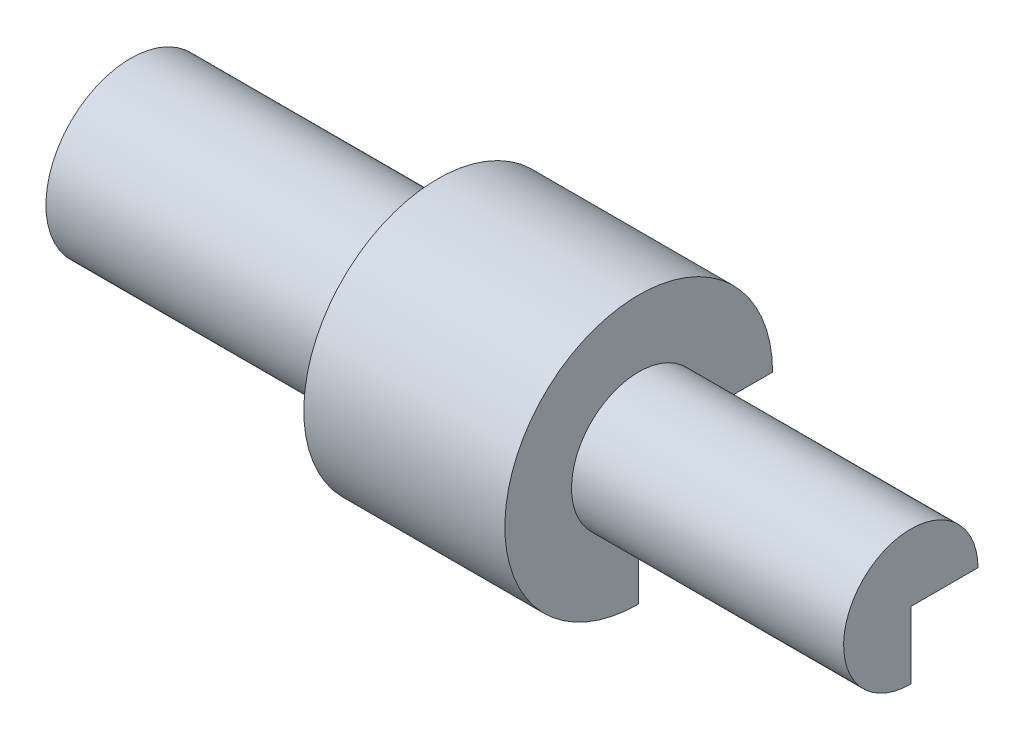
SolidWorks part; units mm, degrees
ref_plane "Front Plane" through (0, 0, 0) normal (0, 0, 1) x (1, 0, 0)
ref_plane "Top Plane" through (0, 0, 0) normal (0, 1, 0) x (1, 0, 0)
ref_plane "Right Plane" through (0, 0, 0) normal (1, 0, 0) x (0, 0, -1)
sketch "Sketch1" plane through (0, 0, 0) normal (0, 1, 0) x (1, 0, 0)
  line L0 (0, 0) -> (0, 32.5503)
  line L1 (0, 32.5503) -> (118.0212, 32.5503)
  line L2 (118.0212, 51.4505) -> (195.3021, 51.4505)
  line L3 (195.3021, 51.4505) -> (195.3021, 25.8303)
  line L4 (118.0212, 32.5503) -> (118.0212, 51.4505)
  line L5 (195.3021, 25.8303) -> (299.8903, 25.8303)
  line L6 (299.8903, 25.8303) -> (299.8903, 0)
  line L7 (0, 0) -> (317.8829, 0) construction
  line L8 (15.1936, 0) -> (15.1936, 18.2011)
  line L9 (15.1936, 18.2011) -> (199.0808, 18.2011)
  line L10 (199.0808, 18.2011) -> (199.0808, 9.1005)
  line L11 (199.0808, 9.1005) -> (279.7251, 9.1005)
  line L12 (279.7251, 9.1005) -> (279.7251, 0)
revolve "Revolve4" add sketch "Sketch1" angle 270 about L7
